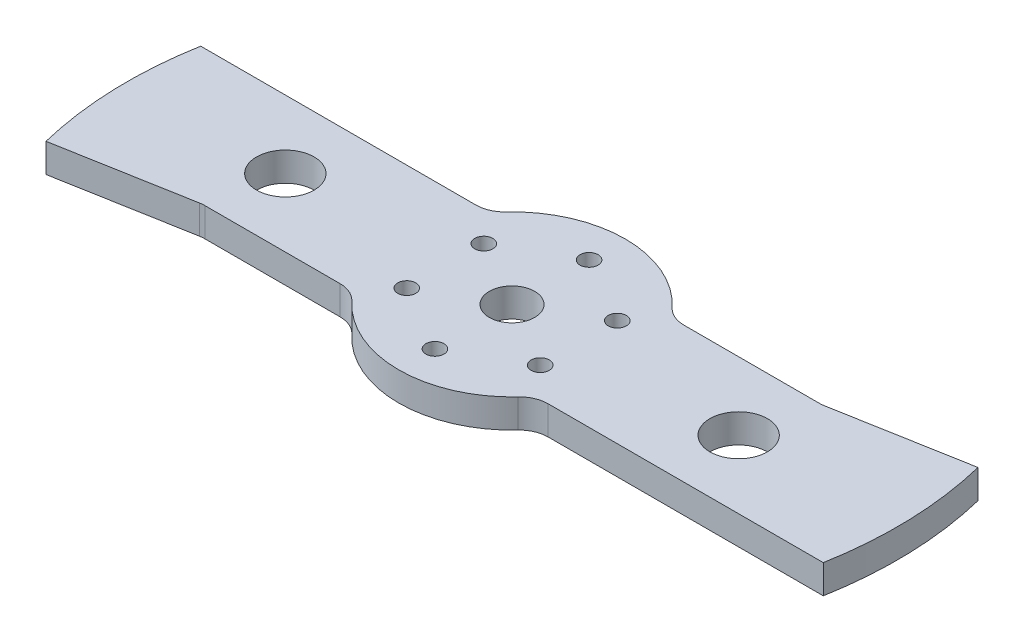
SolidWorks part; units mm, degrees
material "AISI 4340 Acero normalizado"
ref_plane "Alzado" through (0, 0, 0) normal (0, 0, 1) x (1, 0, 0)
ref_plane "Planta" through (0, 0, 0) normal (0, 1, 0) x (1, 0, 0)
ref_plane "Vista lateral" through (0, 0, 0) normal (1, 0, 0) x (0, 0, -1)
sketch "Croquis1" plane through (0, 0, 0) normal (0, 1, 0) x (1, 0, 0)
  line L0 (-22.9565, 15) -> (-83.666, 15)
  line L1 (83.666, -15) -> (22.9565, -15)
  line L3 (53.3112, 15) -> (22.9565, 15)
  line L5 (83.666, -15) -> (-83.666, 15) construction
  line L6 (83.666, 15) -> (-83.666, -15) construction
  line L7 (-22.9565, -15) -> (-53.3112, -15)
  line L8 (-85, 0) -> (85, 0) construction
  line L9 (0, -25) -> (0, 25) construction
  line L10 (-12.0208, -12.0208) -> (12.0208, 12.0208) construction
  line L11 (12.0208, -12.0208) -> (-12.0208, 12.0208) construction
  line L12 (53.3112, 15) -> (82.5544, 20.2428)
  line L13 (-53.3112, -15) -> (-82.5544, -20.2428)
  line L14 (53.3112, -15) -> (53.3112, 15) construction
  line L15 (-53.3112, 15) -> (-53.3112, -15) construction
  circle A0 centre (0, 0) radius 5
  circle A1 centre (0, 0) radius 85 construction
  arc A2 (-83.666, -15) -> (-83.666, 15) centre (0, 0) cw
  arc A3 (83.666, -15) -> (83.666, 15) centre (0, 0) ccw
  arc A4 (-18.3066, -17.0255) -> (18.3066, -17.0255) centre (0, 0) ccw
  arc A5 (18.3066, 17.0255) -> (-18.3066, 17.0255) centre (0, 0) ccw
  circle A6 centre (0, 0) radius 17 construction
  arc A7 (-22.9565, -15) -> (-18.3066, -17.0255) centre (-22.9565, -21.35) cw
  arc A8 (18.3066, -17.0255) -> (22.9565, -15) centre (22.9565, -21.35) cw
  arc A9 (22.9565, 15) -> (18.3066, 17.0255) centre (22.9565, 21.35) cw
  arc A10 (-18.3066, 17.0255) -> (-22.9565, 15) centre (-22.9565, 21.35) cw
  circle A11 centre (0, -17) radius 2 construction
  circle A12 centre (17, 0) radius 2 construction
  circle A13 centre (0, 17) radius 2
  circle A14 centre (-17, 0) radius 2 construction
  circle A15 centre (12.0208, -12.0208) radius 2 construction
  circle A16 centre (-12.0208, -12.0208) radius 2 construction
  circle A17 centre (-12.0208, 12.0208) radius 2 construction
  circle A18 centre (12.0208, 12.0208) radius 2 construction
  arc A19 (-83.666, -15) -> (-82.5544, -20.2428) centre (0, 0) ccw
  arc A20 (82.5544, 20.2428) -> (83.666, 15) centre (0, 0) cw
  circle A21 centre (14.7224, 8.5) radius 2
  circle A22 centre (14.7224, -8.5) radius 2
  circle A23 centre (0, -17) radius 2
  circle A24 centre (-14.7224, -8.5) radius 2
  circle A25 centre (-14.7224, 8.5) radius 2
  point P21 (20, 15)
  point P24 (-20, 15)
  point P50 (0, 0)
  point P51 (-14.7224, 8.5)
  point P61 (0, 0)
  dimension "D1" = 10
  dimension "D2" = 170
  dimension "D3" = 25
  dimension "D5" = 6.35
  dimension "D6" = 4
  dimension "D7" = 8
  dimension "D4" = 30
  dimension "D8" = 45
  dimension "D9" = 6
extrude "Saliente-Extruir1" add sketch "Croquis1" along normal blind 6.35
fillet "Redondeo1" radius 6.35 2 edges at (53.3112, 3.175, -15) (-53.3112, 3.175, 15)
sketch "Croquis2" plane through (0, 6.35, 0) normal (0, 1, 0) x (1, 0, 0)
  line L0 (0, 0) -> (-85, 0) construction
  line L1 (0, 0) -> (85, 0) construction
  arc A0 (-83.666, 15) -> (-82.5544, -20.2428) centre (0, 0) ccw construction
  arc A1 (83.666, -15) -> (82.5544, 20.2428) centre (0, 0) ccw construction
  circle A2 centre (-50, 0) radius 6.35
  circle A3 centre (50, 0) radius 6.35
  dimension "D1" = 50
  dimension "D3" = 12.7
  dimension "D2" = 50
extrude "Cortar-Extruir1" cut sketch "Croquis2" against normal through all
